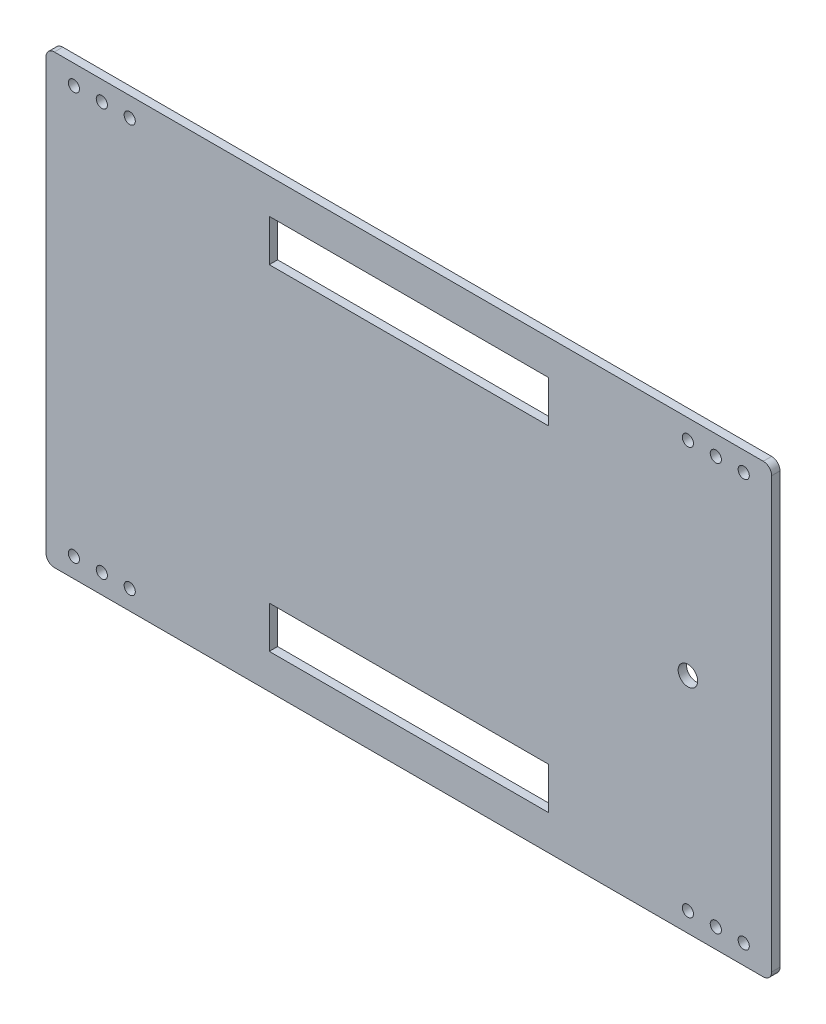
SolidWorks part; units mm, degrees
ref_plane "前视基准面" through (0, 0, 0) normal (0, 0, 1) x (1, 0, 0)
ref_plane "上视基准面" through (0, 0, 0) normal (0, 1, 0) x (1, 0, 0)
ref_plane "右视基准面" through (0, 0, 0) normal (1, 0, 0) x (0, 0, -1)
sketch "Model" plane through (0, 0, 0) normal (0, 0, 1) x (1, 0, 0)
  line L0 (-70, 20) -> (-110, 20)
  line L1 (-70, -20) -> (-70, 20)
  line L2 (-110, -20) -> (-70, -20)
  line L3 (-110, 20) -> (-110, -20)
  line L4 (110, 20) -> (70, 20)
  line L5 (110, -20) -> (110, 20)
  line L6 (70, -20) -> (110, -20)
  line L7 (70, 20) -> (70, -20)
  line L8 (50, 67.5) -> (-50, 67.5)
  line L9 (50, 52.5) -> (50, 67.5)
  line L10 (-50, 52.5) -> (50, 52.5)
  line L11 (-50, 67.5) -> (-50, 52.5)
  line L12 (-50, -67.5) -> (50, -67.5)
  line L13 (-50, -52.5) -> (-50, -67.5)
  line L14 (50, -52.5) -> (-50, -52.5)
  line L15 (50, -67.5) -> (50, -52.5)
  line L16 (28.5432, -28.5432) -> (28.5432, -23.5432)
  line L17 (23.5432, -28.5432) -> (28.5432, -28.5432)
  line L18 (130, -77) -> (130, 77)
  line L19 (127, 80) -> (-127, 80)
  line L20 (-130, 77) -> (-130, -77)
  line L21 (-127, -80) -> (127, -80)
  circle A0 centre (0, 40.4) radius 1.5
  circle A1 centre (40.4, 0) radius 1.5
  circle A2 centre (0, -40.4) radius 1.5
  circle A3 centre (-40.4, 0) radius 1.5
  arc A4 (28.5432, -23.5432) -> (23.5432, -28.5432) centre (0, 0) ccw
  arc A5 (130, 77) -> (127, 80) centre (127, 77) ccw
  arc A6 (-127, 80) -> (-130, 77) centre (-127, 77) ccw
  arc A7 (-130, -77) -> (-127, -80) centre (-127, -77) ccw
  arc A8 (127, -80) -> (130, -77) centre (127, -77) ccw
  circle A9 centre (-110, 73) radius 2
  circle A10 centre (110, 73) radius 2
  circle A11 centre (110, -73) radius 2
  circle A12 centre (-110, -73) radius 2
  circle A13 centre (-120, 73) radius 2
  circle A14 centre (120, 73) radius 2
  circle A15 centre (-120, -73) radius 2
  circle A16 centre (120, -73) radius 2
  circle A17 centre (-100, 73) radius 2
  circle A18 centre (100, 73) radius 2
  circle A19 centre (100, -73) radius 2
  circle A20 centre (-100, -73) radius 2
extrude "凸台-拉伸1" add sketch "Model" along normal blind 3
sketch "草图2" plane through (0, 0, 3) normal (0, 0, 1) x (1, 0, 0)
  line L1 (-48.4599, -44.1133) -> (48.4599, -44.1133)
  line L2 (-48.4599, -44.1133) -> (-48.4599, 44.1133)
  line L3 (-48.4599, 44.1133) -> (48.4599, 44.1133)
  line L4 (48.4599, -44.1133) -> (48.4599, 44.1133)
  line L5 (-48.4599, -44.1133) -> (48.4599, 44.1133) construction
  line L6 (-48.4599, 44.1133) -> (48.4599, -44.1133) construction
  point P0 (0, 0)
extrude "凸台-拉伸2" add sketch "草图2" against normal blind 3
sketch "草图3" plane through (0, 0, 3) normal (0, 0, 1) x (1, 0, 0)
  line L1 (61.2222, -32.2758) -> (116.3408, -32.2758)
  line L2 (61.2222, -32.2758) -> (61.2222, 29.1314)
  line L3 (61.2222, 29.1314) -> (116.3408, 29.1314)
  line L4 (116.3408, -32.2758) -> (116.3408, 29.1314)
  line L5 (61.2222, -32.2758) -> (116.3408, 29.1314) construction
  line L6 (61.2222, 29.1314) -> (116.3408, -32.2758) construction
  point P0 (88.7815, -1.5722)
extrude "凸台-拉伸3" add sketch "草图3" against normal blind 3
sketch "草图4" plane through (0, 0, 3) normal (0, 0, 1) x (1, 0, 0)
  line L0 (130, 0) -> (100, 0)
  line L1 (130, -77) -> (130, 77) construction
  circle A0 centre (100, 0) radius 3.5
  dimension "D2" = 7
  dimension "D1" = 30
extrude "切除-拉伸4" cut sketch "草图4" against normal blind 3 contours A0
sketch "草图5" plane through (0, 0, 3) normal (0, 0, 1) x (1, 0, 0)
  line L1 (-64.9215, -29.5014) -> (-115.9708, -29.5014)
  line L2 (-64.9215, -29.5014) -> (-64.9215, 29.5014)
  line L3 (-64.9215, 29.5014) -> (-115.9708, 29.5014)
  line L4 (-115.9708, -29.5014) -> (-115.9708, 29.5014)
  line L5 (-64.9215, -29.5014) -> (-115.9708, 29.5014) construction
  line L6 (-64.9215, 29.5014) -> (-115.9708, -29.5014) construction
  point P0 (-90.4462, 0)
extrude "凸台-拉伸4" add sketch "草图5" against normal blind 3
